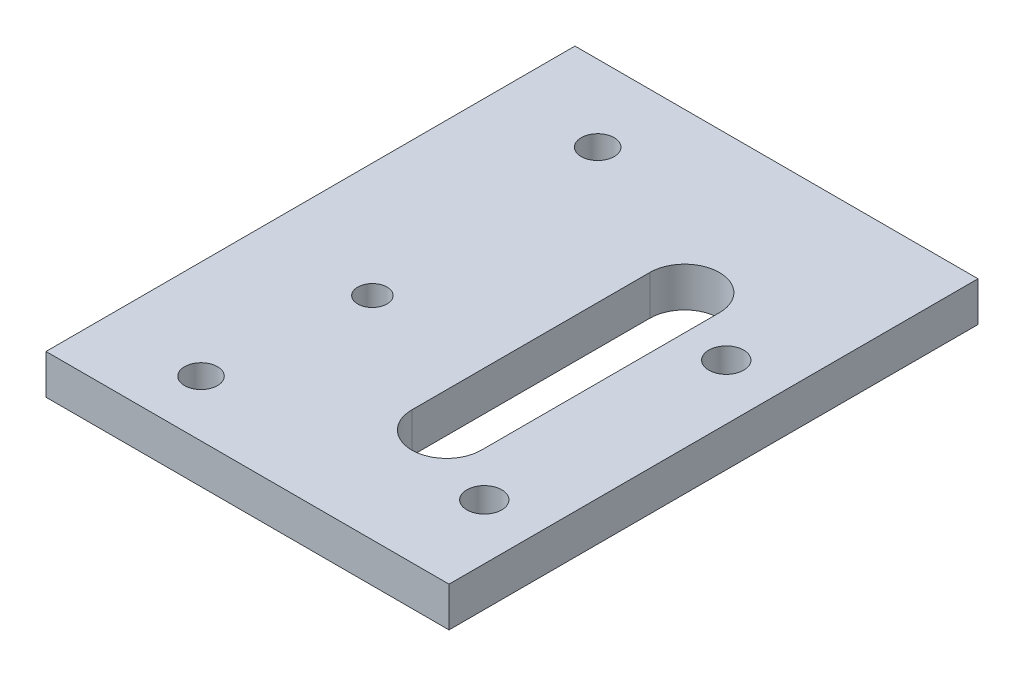
SolidWorks part; units mm, degrees
ref_plane "Front Plane" through (0, 0, 0) normal (0, 0, 1) x (1, 0, 0)
ref_plane "Top Plane" through (0, 0, 0) normal (0, 1, 0) x (1, 0, 0)
ref_plane "Right Plane" through (0, 0, 0) normal (1, 0, 0) x (0, 0, -1)
sketch "Sketch1" plane through (0, 0, 0) normal (0, 1, 0) x (1, 0, 0)
  line L1 (0, 0) -> (50.8, 0)
  line L2 (0, 0) -> (0, 66.675)
  line L3 (0, 66.675) -> (50.8, 66.675)
  line L4 (50.8, 0) -> (50.8, 66.675)
  dimension "D1" = 50.8
  dimension "D2" = 66.675
extrude "Boss-Extrude1" add sketch "Sketch1" along normal blind 5
sketch "Sketch2" plane through (0, 5, 0) normal (0, 1, 0) x (1, 0, 0)
  line L0 (0, 66.675) -> (0, 0) construction
  line L1 (50.8, 66.675) -> (0, 66.675) construction
  circle A0 centre (12.465, 57.075) radius 2.075
  circle A1 centre (12.465, 7.075) radius 2.075
  circle A2 centre (14.465, 26.675) radius 1.85
  dimension "D1" = 4.15
  dimension "D3" = 9.6
  dimension "D4" = 50
  dimension "D8" = 4.15
  dimension "D11" = 3.7
  dimension "D16" = 2
  dimension "D17" = 30.4
  dimension "D2" = 12.465
extrude "Cut-Extrude1" cut sketch "Sketch2" against normal through all
sketch "Sketch3" plane through (0, 5, 0) normal (0, 1, 0) x (1, 0, 0)
  line L5 (50.8, 66.675) -> (0, 66.675) construction
  line L7 (0, 66.675) -> (0, 0) construction
  circle A0 centre (43.82, 41.925) radius 2.2
  circle A1 centre (43.82, 11.425) radius 2.2
  dimension "D1" = 4.4
  dimension "D2" = 4.4
  dimension "D4" = 30.5
  dimension "D3" = 24.75
  dimension "D5" = 43.82
extrude "Cut-Extrude2" cut sketch "Sketch3" against normal up to next
sketch "Sketch4" plane through (0, 5, 0) normal (0, 1, 0) x (1, 0, 0)
  line L0 (33.82, 46.675) -> (33.82, 16.675) construction
  line L1 (38.21, 46.675) -> (38.21, 16.675)
  line L2 (29.43, 46.675) -> (29.43, 16.675)
  line L11 (50.8, 66.675) -> (0, 66.675) construction
  arc A0 (38.21, 46.675) -> (29.43, 46.675) centre (33.82, 46.675) ccw
  arc A1 (29.43, 16.675) -> (38.21, 16.675) centre (33.82, 16.675) ccw
  circle A3 centre (43.82, 41.925) radius 2.2 construction
  point P2 (33.82, 31.675)
  dimension "D1" = 10
  dimension "D2" = 30
  dimension "D4" = 20
extrude "Cut-Extrude3" cut sketch "Sketch4" against normal up to next
